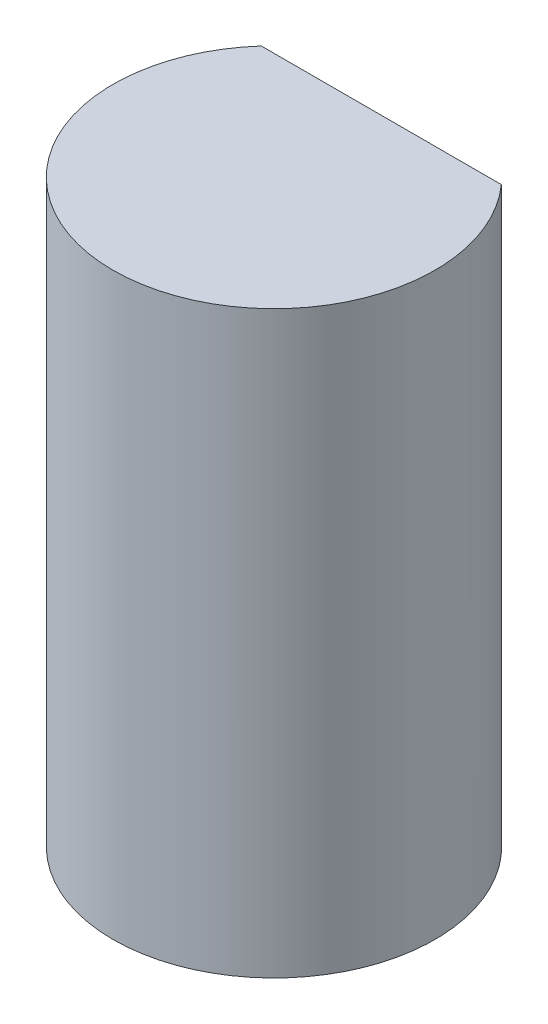
SolidWorks part; units mm, degrees
material "不锈钢 (铁素体)"
ref_plane "前视基准面" through (0, 0, 0) normal (0, 0, 1) x (1, 0, 0)
ref_plane "上视基准面" through (0, 0, 0) normal (0, 1, 0) x (1, 0, 0)
ref_plane "右视基准面" through (0, 0, 0) normal (1, 0, 0) x (0, 0, -1)
sketch "草图1" plane through (0, 0, 0) normal (0, 1, 0) x (1, 0, 0)
  circle A0 centre (0, 0) radius 1.5
extrude "凸台-拉伸1" add sketch "草图1" along normal blind 5.4
sketch "草图2" plane through (0, 5.4, 0) normal (0, 1, 0) x (1, 0, 0)
  line L0 (-1.118, 1) -> (1.118, 1)
  circle A0 centre (0, 0) radius 1.5 construction
  arc A1 (1.118, 1) -> (-1.118, 1) centre (0, 0) ccw
  dimension "D1" = 1
extrude "切除-拉伸1" cut sketch "草图2" against normal blind 3.7
